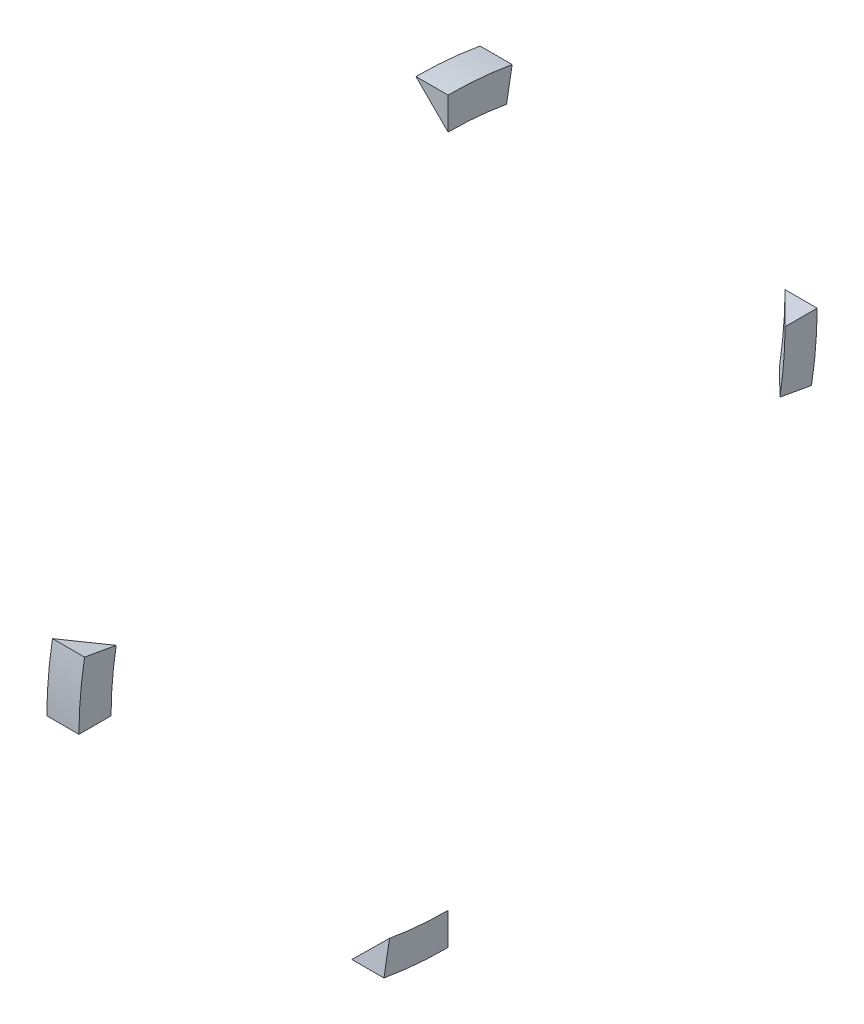
SolidWorks part; units mm, degrees
material "Hexcel AS4C (3000 Filaments)"
ref_plane "Front Plane" through (0, 0, 0) normal (0, 0, 1) x (1, 0, 0)
ref_plane "Top Plane" through (0, 0, 0) normal (0, 1, 0) x (1, 0, 0)
ref_plane "Right Plane" through (0, 0, 0) normal (1, 0, 0) x (0, 0, -1)
sketch "Sketch1" plane through (0, 0, 0) normal (0, 0, 1) x (1, 0, 0)
  line L0 (0, 0) -> (-12.7, 0)
  line L1 (-12.7, 0) -> (0, -12.7)
  line L2 (0, -12.7) -> (0, 0)
  line L3 (0, -12.7) -> (0, -146.05) construction
  line L4 (0, -146.05) -> (-86.1056, -146.05) construction
  dimension "D1" = 12.7
  dimension "D2" = 12.7
  dimension "D3" = 133.35
revolve "Revolve1" add sketch "Sketch1" angle 10 about L4
sketch3d "3DSketch1"
  line L0 (0, -12.7, 0) -> (0, -146.05, 0) construction
  line L1 (0, -146.05, 0) -> (-94.3391, -146.05, 0) construction
  dimension "D1" = 133.35
pattern_circular "CirPattern1" count 4 every 90 about axis through (0, -146.05, 0) along (-1, 0, 0) of bodies 101
